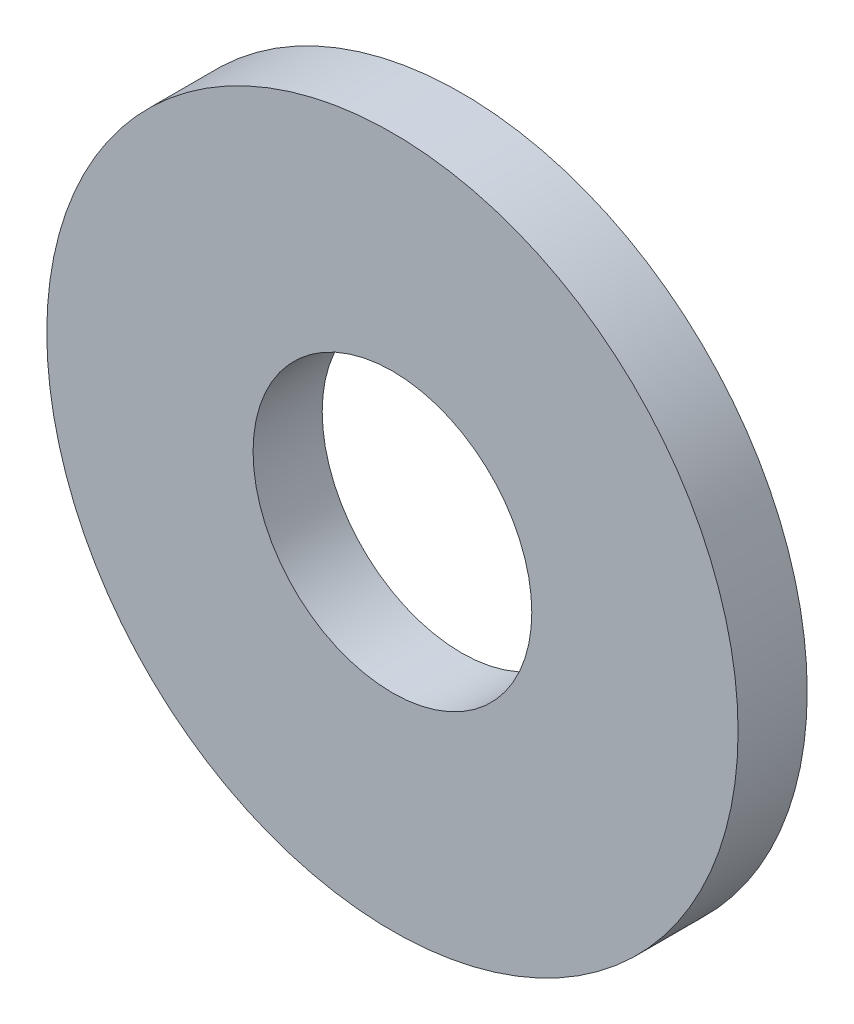
SolidWorks part; units mm, degrees
material "Tin Bearing Bronze"
ref_plane "Front Plane" through (0, 0, 0) normal (0, 0, 1) x (1, 0, 0)
ref_plane "Top Plane" through (0, 0, 0) normal (0, 1, 0) x (1, 0, 0)
ref_plane "Right Plane" through (0, 0, 0) normal (1, 0, 0) x (0, 0, -1)
sketch "Sketch1" plane through (0, 0, 0) normal (0, 0, 1) x (1, 0, 0)
  circle A0 centre (0, 0) radius 7.9375
  circle A1 centre (0, 0) radius 3.2004
  dimension "D1" = 15.875
  dimension "ID" = 6.4008
extrude "Extrude1" add sketch "Sketch1" along normal mid plane 1.5875
sketch "Sketch2" plane through (0, 0, 0) normal (1, 0, 0) x (0, 0, -1)
  line L0 (-0.7937, -3.2004) -> (0.7937, -3.2004) construction
  line L3 (0.7937, 3.2004) -> (-0.7937, 3.2004) construction
  line L5 (-0.7937, -3.2004) -> (0.7937, -3.2004)
  line L6 (0.7937, 3.2004) -> (-0.7937, 3.2004)
sketch "Sketch4" plane through (0, 0, 0.7937) normal (0, 0, 1) x (1, 0, 0)
  line L0 (0, 0) -> (-2.263, 2.263)
  line L1 (0, -0.8731) -> (0, 0.8731) construction
  circle A0 centre (0, 0) radius 3.2004 construction
  dimension "D1" = 45
